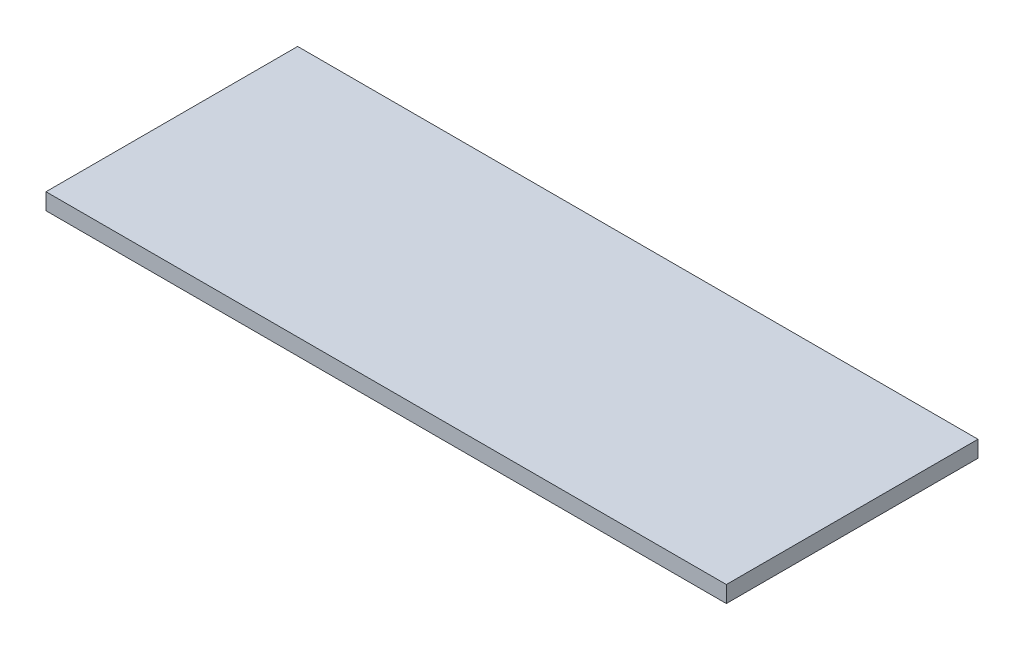
SolidWorks part; units mm, degrees
material "PTFE (general)"
ref_plane "Front Plane" through (0, 0, 0) normal (0, 0, 1) x (1, 0, 0)
ref_plane "Top Plane" through (0, 0, 0) normal (0, 1, 0) x (1, 0, 0)
ref_plane "Right Plane" through (0, 0, 0) normal (1, 0, 0) x (0, 0, -1)
sketch "Sketch1" plane through (0, 0, 0) normal (0, 1, 0) x (1, 0, 0)
  line L1 (0, 0) -> (66, 0)
  line L2 (0, 0) -> (0, 24.412)
  line L3 (0, 24.412) -> (66, 24.412)
  line L4 (66, 0) -> (66, 24.412)
extrude "Extrude1" add sketch "Sketch1" along normal blind 1.6
